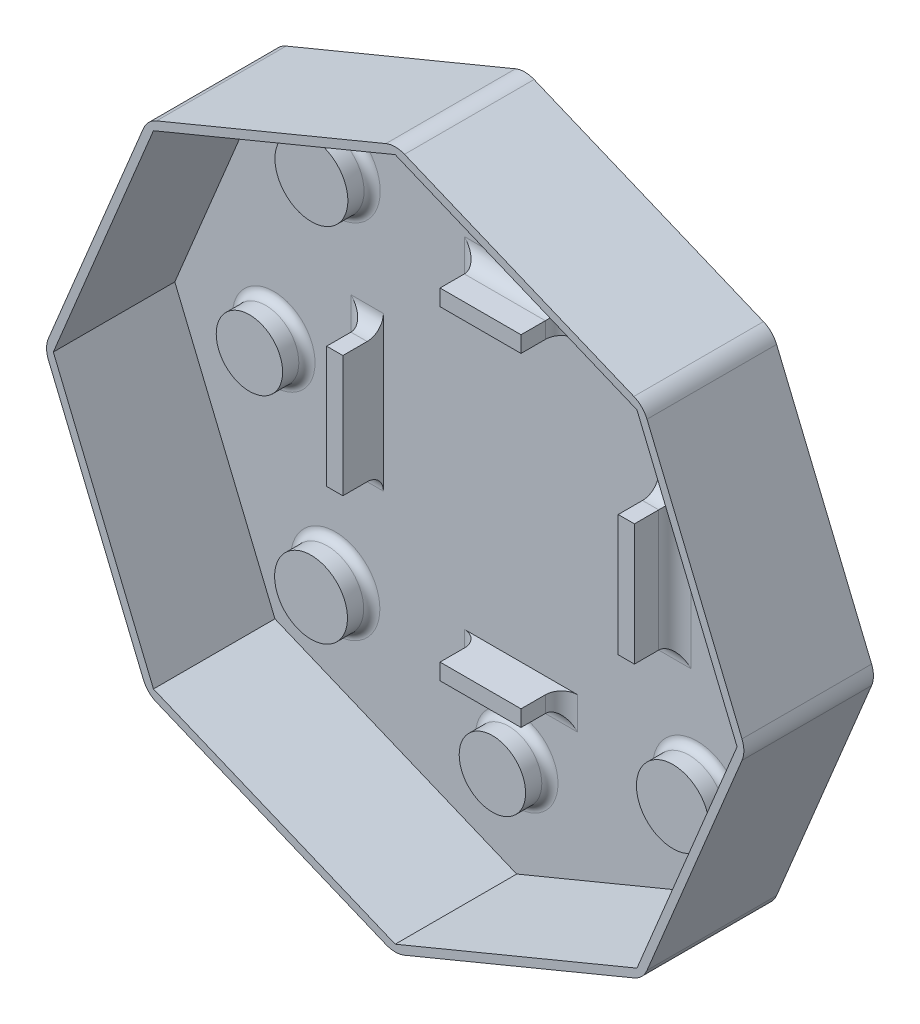
SolidWorks part; units mm, degrees
ref_plane "Plan de face" through (0, 0, 0) normal (0, 0, 1) x (1, 0, 0)
ref_plane "Plan de dessus" through (0, 0, 0) normal (0, 1, 0) x (1, 0, 0)
ref_plane "Plan de droite" through (0, 0, 0) normal (1, 0, 0) x (0, 0, -1)
sketch "Esquisse1" plane through (0, 0, 0) normal (0, 0, 1) x (1, 0, 0)
  line L0 (0, -43.2957) -> (30.6147, -30.6147)
  line L1 (43.2957, 0) -> (30.6147, 30.6147)
  line L2 (30.6147, 30.6147) -> (0, 43.2957)
  line L3 (0, 43.2957) -> (-30.6147, 30.6147)
  line L4 (-30.6147, 30.6147) -> (-43.2957, 0)
  line L5 (-43.2957, 0) -> (-30.6147, -30.6147)
  line L6 (-30.6147, -30.6147) -> (0, -43.2957)
  line L7 (30.6147, -30.6147) -> (43.2957, 0)
  circle A0 centre (0, 0) radius 40 construction
  dimension "D1" = 80
extrude "Boss.-Extru.1" add sketch "Esquisse1" along normal blind 10
sketch "Esquisse2" plane through (0, 0, 0) normal (0, 0, -1) x (-1, 0, 0)
  line L0 (0, 0) -> (0, 46.6475) construction
  line L1 (0, 0) -> (47.64, 0) construction
  circle A4 centre (0, 0) radius 30 construction
  circle A5 centre (0, 30) radius 3.1
  circle A6 centre (30, 0) radius 3.1
  circle A7 centre (0, -30) radius 3.1
  circle A8 centre (-30, 0) radius 3.1
extrude "Enlèv. mat.-Extru.1" cut sketch "Esquisse2" against normal blind 3
shell "Coque2" thickness 1
sketch "Esquisse4" plane through (0, 0, 1) normal (0, 0, 1) x (1, 0, 0)
  line L0 (0, 42.2133) -> (0, -42.2133) construction
  line L1 (-42.2133, 0) -> (42.2133, 0) construction
  line L2 (-29.8493, 29.8493) -> (-42.2133, 0) construction
  line L3 (-29.8493, 29.8493) -> (29.8493, -29.8493) construction
  line L4 (29.8493, 29.8493) -> (-29.8493, -29.8493) construction
sketch "Esquisse5" plane through (0, 0, 1) normal (0, 0, 1) x (1, 0, 0)
  circle A0 centre (-22.3489, 22.3691) radius 4.5
  circle A1 centre (-22.3939, -22.3102) radius 4.5
  circle A2 centre (22.2854, -22.3551) radius 4.5
  circle A3 centre (22.3303, 22.3242) radius 4.5
extrude "Boss.-Extru.3" add sketch "Esquisse5" along normal up to surface (3 mm away) up to face at (-4.1, 30, 4)
fillet "Congé1" radius 3 8 edges at (-30.6147, 30.6147, 5) (-43.2957, 0, 5) (-30.6147, -30.6147, 5) (0, -43.2957, 5) (30.6147, -30.6147, 5) (43.2957, 0, 5) (30.6147, 30.6147, 5) (0, 43.2957, 5)
fillet "Congé4" radius 1 8 edges at (26.8303, 22.3242, 1) (34.1, 0, 1) (26.7854, -22.3551, 1) (4.1, -30, 1) (-17.8939, -22.3102, 1) (-25.9, 0, 1) (-17.8489, 22.3691, 1) (4.1, 30, 1)
sketch "Esquisse6" plane through (0, 0, 1) normal (0, 0, 1) x (1, 0, 0)
  line L0 (-18.4645, -7.5) -> (-16.4645, -7.5)
  line L1 (-18.4645, -7.5) -> (-18.4645, 7.5)
  line L2 (-16.4645, -7.5) -> (-16.4645, 7.5)
  line L3 (-18.4645, 7.5) -> (-16.4645, 7.5)
  line L4 (-18.4645, -7.5) -> (-16.4645, 7.5) construction
  line L5 (-16.4645, -7.5) -> (-18.4645, 7.5) construction
  line L6 (-16.4645, -17.278) -> (-16.4645, 16.722) construction
  line L7 (-17.4645, 0) -> (0, 0) construction
  line L8 (0.5355, 16.722) -> (0.5355, -17.278) construction
  line L9 (15.5355, 16.722) -> (-14.4645, 16.722) construction
  line L10 (-14.4645, -17.278) -> (15.5355, -17.278) construction
  line L11 (17.5355, -7.5) -> (17.5355, 7.5)
  line L12 (19.5355, 7.5) -> (17.5355, 7.5)
  line L13 (19.5355, -7.5) -> (19.5355, 7.5)
  line L14 (19.5355, -7.5) -> (17.5355, -7.5)
  line L15 (17.5355, -7.5) -> (19.5355, 7.5) construction
  line L16 (19.5355, -7.5) -> (17.5355, 7.5) construction
  line L17 (-4.4645, 20.722) -> (-4.4645, 18.722)
  line L18 (-4.4645, 20.722) -> (5.5355, 20.722)
  line L19 (-4.4645, 18.722) -> (5.5355, 18.722)
  line L20 (5.5355, 20.722) -> (5.5355, 18.722)
  line L21 (-4.4645, 20.722) -> (5.5355, 18.722) construction
  line L22 (-4.4645, 18.722) -> (5.5355, 20.722) construction
  line L23 (-14.4645, 18.722) -> (15.5355, 18.722) construction
  line L24 (0.5355, 16.722) -> (0.5355, 19.722) construction
  line L25 (-14.4645, -0.278) -> (15.5355, -0.278) construction
  line L26 (-14.4645, 16.722) -> (-14.4645, -17.278) construction
  line L27 (15.5355, -17.278) -> (15.5355, 16.722) construction
  line L28 (-4.4645, -19.278) -> (5.5355, -19.278)
  line L29 (5.5355, -21.278) -> (5.5355, -19.278)
  line L30 (-4.4645, -21.278) -> (5.5355, -21.278)
  line L31 (-4.4645, -21.278) -> (-4.4645, -19.278)
  point P1 (-17.4645, 0)
  point P21 (0.5355, 19.722)
  dimension "D1" = 2
  dimension "D2" = 15
  dimension "D3" = 0
  dimension "D4" = 2
  dimension "D5" = 0
  dimension "D6" = 10
extrude "Boss.-Extru.4" add sketch "Esquisse6" along normal blind 5
fillet "Congé5" radius 2 12 edges at (-4.4645, 19.722, 1) (5.5355, 19.722, 1) (0.5355, 20.722, 1) (18.5355, 7.5, 1) (19.5355, 0, 1) (18.5355, -7.5, 1) (5.5355, -20.278, 1) (0.5355, -21.278, 1) (-4.4645, -20.278, 1) (-17.4645, -7.5, 1) (-17.4645, 7.5, 1) (-18.4645, 0, 1)
sketch "Esquisse7" plane through (0, 0, 10) normal (0, 0, 1) x (1, 0, 0)
  line L16 (-1.1481, 42.8202) -> (-29.4666, 31.0902)
  line L17 (-31.0902, 29.4666) -> (-42.8202, 1.1481)
  line L18 (-42.8202, -1.1481) -> (-31.0902, -29.4666)
  line L19 (-29.4666, -31.0902) -> (-1.1481, -42.8202)
  line L20 (1.1481, -42.8202) -> (29.4666, -31.0902)
  line L21 (31.0902, -29.4666) -> (42.8202, -1.1481)
  line L22 (42.8202, 1.1481) -> (31.0902, 29.4666)
  line L23 (29.4666, 31.0902) -> (1.1481, 42.8202)
  line L24 (-1.1481, 42.8202) -> (-29.4666, 31.0902)
  line L25 (-31.0902, 29.4666) -> (-42.8202, 1.1481)
  line L26 (-42.8202, -1.1481) -> (-31.0902, -29.4666)
  line L27 (-29.4666, -31.0902) -> (-1.1481, -42.8202)
  line L28 (1.1481, -42.8202) -> (29.4666, -31.0902)
  line L29 (31.0902, -29.4666) -> (42.8202, -1.1481)
  line L30 (42.8202, 1.1481) -> (31.0902, 29.4666)
  line L31 (29.4666, 31.0902) -> (1.1481, 42.8202)
  line L68 (-42.2133, 0) -> (-29.8493, -29.8493)
  line L69 (-29.8493, -29.8493) -> (0, -42.2133)
  line L70 (0, -42.2133) -> (29.8493, -29.8493)
  line L71 (29.8493, -29.8493) -> (42.2133, 0)
  line L72 (42.2133, 0) -> (29.8493, 29.8493)
  line L73 (29.8493, 29.8493) -> (0, 42.2133)
  line L74 (-29.8493, 29.8493) -> (-42.2133, 0)
  line L75 (0, 42.2133) -> (-29.8493, 29.8493)
  line L76 (-42.2133, 0) -> (-29.8493, -29.8493)
  line L77 (-29.8493, -29.8493) -> (0, -42.2133)
  line L78 (0, -42.2133) -> (29.8493, -29.8493)
  line L79 (29.8493, -29.8493) -> (42.2133, 0)
  line L80 (42.2133, 0) -> (29.8493, 29.8493)
  line L81 (29.8493, 29.8493) -> (0, 42.2133)
  line L82 (-29.8493, 29.8493) -> (-42.2133, 0)
  line L83 (0, 42.2133) -> (-29.8493, 29.8493)
  arc A16 (-29.4666, 31.0902) -> (-31.0902, 29.4666) centre (-28.3186, 28.3186) ccw
  arc A17 (-42.8202, 1.1481) -> (-42.8202, -1.1481) centre (-40.0485, 0) ccw
  arc A18 (-31.0902, -29.4666) -> (-29.4666, -31.0902) centre (-28.3186, -28.3186) ccw
  arc A19 (-1.1481, -42.8202) -> (1.1481, -42.8202) centre (0, -40.0485) ccw
  arc A20 (29.4666, -31.0902) -> (31.0902, -29.4666) centre (28.3186, -28.3186) ccw
  arc A21 (42.8202, -1.1481) -> (42.8202, 1.1481) centre (40.0485, 0) ccw
  arc A22 (31.0902, 29.4666) -> (29.4666, 31.0902) centre (28.3186, 28.3186) ccw
  arc A23 (1.1481, 42.8202) -> (-1.1481, 42.8202) centre (0, 40.0485) ccw
  arc A24 (-29.4666, 31.0902) -> (-31.0902, 29.4666) centre (-28.3186, 28.3186) ccw
  arc A25 (-42.8202, 1.1481) -> (-42.8202, -1.1481) centre (-40.0485, 0) ccw
  arc A26 (-31.0902, -29.4666) -> (-29.4666, -31.0902) centre (-28.3186, -28.3186) ccw
  arc A27 (-1.1481, -42.8202) -> (1.1481, -42.8202) centre (0, -40.0485) ccw
  arc A28 (29.4666, -31.0902) -> (31.0902, -29.4666) centre (28.3186, -28.3186) ccw
  arc A29 (42.8202, -1.1481) -> (42.8202, 1.1481) centre (40.0485, 0) ccw
  arc A30 (31.0902, 29.4666) -> (29.4666, 31.0902) centre (28.3186, 28.3186) ccw
  arc A31 (1.1481, 42.8202) -> (-1.1481, 42.8202) centre (0, 40.0485) ccw
  dimension "D1" = 0
  dimension "D2" = 0
extrude "Boss.-Extru.5" add sketch "Esquisse7" along normal blind 6
